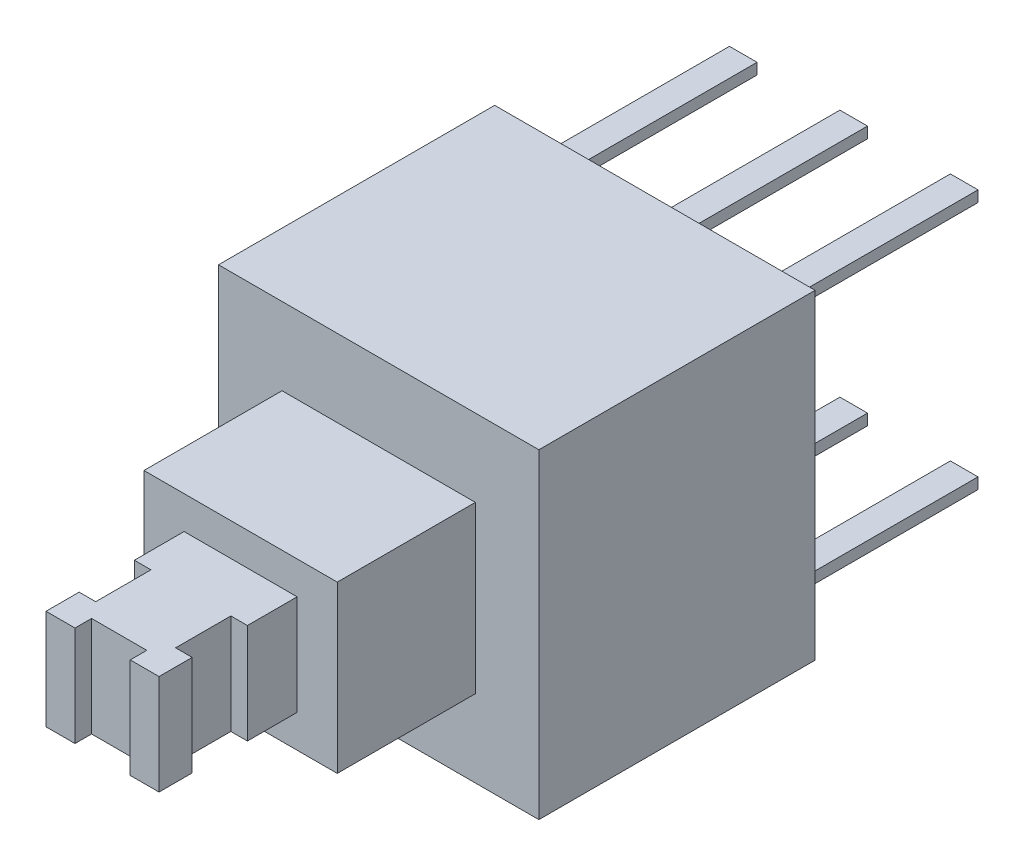
SolidWorks part; units mm, degrees
ref_plane "Front Plane" through (0, 0, 0) normal (0, 0, 1) x (1, 0, 0)
ref_plane "Top Plane" through (0, 0, 0) normal (0, 1, 0) x (1, 0, 0)
ref_plane "Right Plane" through (0, 0, 0) normal (1, 0, 0) x (0, 0, -1)
sketch "Sketch1" plane through (0, 0, 0) normal (0, 0, 1) x (1, 0, 0)
  line L1 (0, 0) -> (5.8, 0)
  line L2 (0, 0) -> (0, 5.8)
  line L3 (0, 5.8) -> (5.8, 5.8)
  line L4 (5.8, 0) -> (5.8, 5.8)
  dimension "D1" = 5.8
  dimension "D2" = 5.8
extrude "Boss-Extrude2" add sketch "Sketch1" along normal blind 5
sketch "Sketch3" plane through (0, 0, 5) normal (0, 0, 1) x (1, 0, 0)
  line L0 (1.15, 4.4) -> (1.15, 1.4)
  line L1 (1.15, 1.4) -> (4.65, 1.4)
  line L2 (4.65, 1.4) -> (4.65, 4.4)
  line L3 (4.65, 4.4) -> (1.15, 4.4)
  line L4 (0, 5.8) -> (0, 0) construction
  line L5 (0, 0) -> (5.8, 0) construction
  point P6 (0, 2.9)
  point P7 (1.15, 2.9)
  point P10 (2.9, 0)
  point P11 (2.9, 1.4)
  dimension "D1" = 3.5
  dimension "D2" = 3
extrude "Boss-Extrude3" add sketch "Sketch3" along normal blind 2.5
sketch "Sketch4" plane through (0, 0, 7.5) normal (0, 0, 1) x (1, 0, 0)
  line L0 (1.8768, 1.9941) -> (3.9232, 1.9941)
  line L1 (3.9232, 1.9941) -> (3.9232, 3.8059)
  line L2 (3.9232, 3.8059) -> (1.8768, 3.8059)
  line L3 (1.8768, 3.8059) -> (1.8768, 1.9941)
  line L4 (1.15, 1.4) -> (4.65, 1.4) construction
  line L5 (1.15, 4.4) -> (1.15, 1.4) construction
  point P6 (2.9, 1.4)
  point P7 (2.9, 1.9941)
  point P10 (1.15, 2.9)
  point P11 (1.8768, 2.9)
extrude "Boss-Extrude4" add sketch "Sketch4" along normal blind 2.5
sketch "Sketch5" plane through (0, 0, 0) normal (0, 0, -1) x (-1, 0, 0)
  line L0 (-6.4508, 5.15) -> (0.8611, 5.15) construction
  line L1 (-5.8, 5.8) -> (0, 5.8) construction
  line L2 (-6.1354, 0.65) -> (0.6185, 0.65) construction
  line L3 (0, 0) -> (-5.8, 0) construction
  line L4 (-2.9, 0) -> (-2.9, 5.8) construction
  line L5 (-4.9, 5.8) -> (-4.9, 0) construction
  line L6 (-0.9, 5.8) -> (-0.9, 0) construction
  line L8 (-5.15, 5.25) -> (-4.65, 5.25)
  line L9 (-5.15, 5.25) -> (-5.15, 5.05)
  line L10 (-5.15, 5.05) -> (-4.65, 5.05)
  line L11 (-4.65, 5.25) -> (-4.65, 5.05)
  line L12 (-3.15, 5.25) -> (-2.65, 5.25)
  line L13 (-3.15, 5.25) -> (-3.15, 5.05)
  line L14 (-3.15, 5.05) -> (-2.65, 5.05)
  line L15 (-2.65, 5.25) -> (-2.65, 5.05)
  line L16 (-1.15, 5.25) -> (-0.65, 5.25)
  line L17 (-1.15, 5.25) -> (-1.15, 5.05)
  line L18 (-1.15, 5.05) -> (-0.65, 5.05)
  line L19 (-0.65, 5.25) -> (-0.65, 5.05)
  line L20 (-1.15, 0.75) -> (-0.65, 0.75)
  line L21 (-1.15, 0.75) -> (-1.15, 0.55)
  line L22 (-1.15, 0.55) -> (-0.65, 0.55)
  line L23 (-0.65, 0.75) -> (-0.65, 0.55)
  line L24 (-3.15, 0.75) -> (-2.65, 0.75)
  line L25 (-3.15, 0.75) -> (-3.15, 0.55)
  line L26 (-3.15, 0.55) -> (-2.65, 0.55)
  line L27 (-2.65, 0.75) -> (-2.65, 0.55)
  line L28 (-5.15, 0.75) -> (-4.65, 0.75)
  line L29 (-5.15, 0.75) -> (-5.15, 0.55)
  line L30 (-5.15, 0.55) -> (-4.65, 0.55)
  line L31 (-4.65, 0.75) -> (-4.65, 0.55)
  point P18 (-4.65, 5.15)
  point P19 (-4.9, 5.05)
  point P24 (-2.9, 5.05)
  point P25 (-3.15, 5.15)
  point P30 (-0.9, 5.05)
  point P31 (-1.15, 5.15)
  point P44 (-0.9, 0.55)
  point P45 (-1.15, 0.65)
  point P46 (-2.9, 0.55)
  point P47 (-3.15, 0.65)
  point P48 (-4.9, 0.55)
  point P49 (-5.15, 0.65)
  dimension "D1" = 0.65
  dimension "D2" = 0.65
  dimension "D3" = 2
  dimension "D4" = 2
  dimension "D5" = 0.5
  dimension "D6" = 0.2
  dimension "D7" = 0.5
  dimension "D8" = 0.2
  dimension "D9" = 0.5
  dimension "D10" = 0.2
  dimension "D11" = 0.5
  dimension "D12" = 0.5
  dimension "D13" = 0.5
  dimension "D14" = 0.2
  dimension "D15" = 0.2
  dimension "D16" = 0.2
extrude "Boss-Extrude5" add sketch "Sketch5" along normal blind 3.6
sketch "Sketch6" plane through (0, 1.9941, 0) normal (0, -1, 0) x (1, 0, 0)
  line L0 (1.8768, 10) -> (3.9232, 10) construction
  line L1 (2.4018, 10) -> (3.4018, 10)
  line L2 (2.4018, 10) -> (2.4018, 9.7)
  line L3 (2.4018, 9.7) -> (3.4018, 9.7)
  line L4 (3.4018, 10) -> (3.4018, 9.7)
  line L5 (1.8768, 10) -> (1.8768, 7.5) construction
  line L6 (1.8768, 9.4) -> (2.1768, 9.4)
  line L7 (1.8768, 9.4) -> (1.8768, 8.4)
  line L8 (1.8768, 8.4) -> (2.1768, 8.4)
  line L9 (2.1768, 9.4) -> (2.1768, 8.4)
  line L10 (3.9232, 10) -> (3.9232, 7.5) construction
  line L11 (3.9232, 9.4) -> (3.6232, 9.4)
  line L12 (3.9232, 9.4) -> (3.9232, 8.4)
  line L13 (3.9232, 8.4) -> (3.6232, 8.4)
  line L14 (3.6232, 9.4) -> (3.6232, 8.4)
  dimension "D1" = 0.3
  dimension "D2" = 0.3
  dimension "D3" = 0.3
  dimension "D4" = 1
  dimension "D5" = 1
  dimension "D6" = 1
  dimension "D7" = 0.6
  dimension "D8" = 0.6
  dimension "D9" = 0.525
extrude "Cut-Extrude1" cut sketch "Sketch6" against normal blind 2
